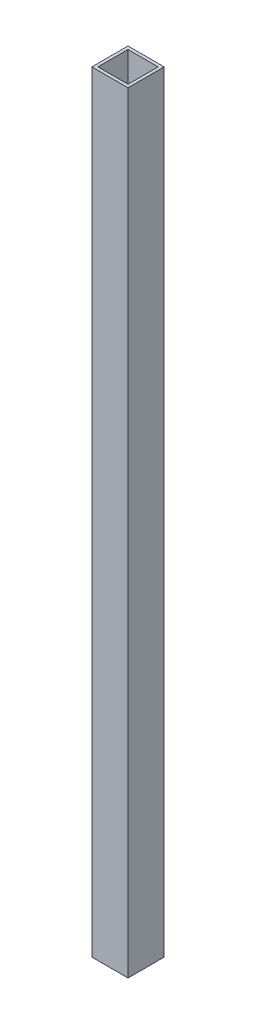
SolidWorks part; units mm, degrees
ref_plane "Alzado" through (0, 0, 0) normal (0, 0, 1) x (1, 0, 0)
ref_plane "Planta" through (0, 0, 0) normal (0, 1, 0) x (1, 0, 0)
ref_plane "Vista lateral" through (0, 0, 0) normal (1, 0, 0) x (0, 0, -1)
sketch "Croquis2" plane through (0, 0, 0) normal (0, 1, 0) x (1, 0, 0)
  line L1 (9.525, 9.525) -> (-9.525, 9.525)
  line L2 (9.525, 9.525) -> (9.525, -9.525)
  line L3 (9.525, -9.525) -> (-9.525, -9.525)
  line L4 (-9.525, 9.525) -> (-9.525, -9.525)
  line L5 (9.525, 9.525) -> (-9.525, -9.525) construction
  line L6 (9.525, -9.525) -> (-9.525, 9.525) construction
  line L10 (-7.9375, 7.9375) -> (-7.9375, -7.9375)
  line L11 (7.9375, -7.9375) -> (-7.9375, -7.9375)
  line L12 (7.9375, 7.9375) -> (7.9375, -7.9375)
  line L13 (7.9375, 7.9375) -> (-7.9375, 7.9375)
  point P0 (0, 0)
  dimension "D1" = 19.05
  dimension "D2" = 19.05
  dimension "D3" = 1.5875
extrude "Saliente-Extruir1" add sketch "Croquis2" along normal blind 406.4
